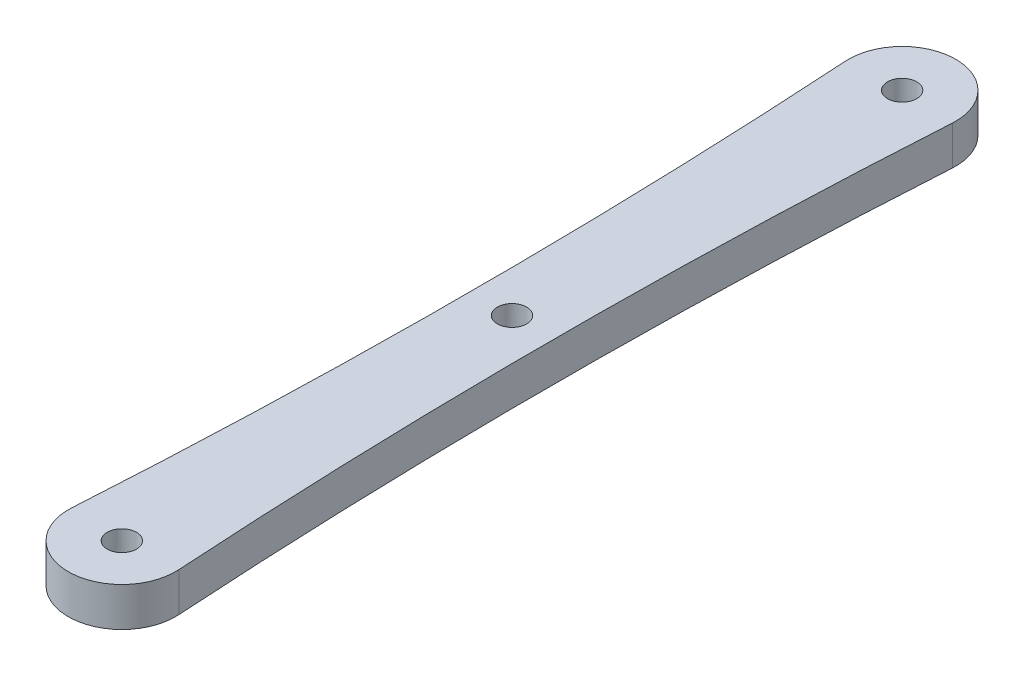
SolidWorks part; units mm, degrees
ref_plane "Front Plane" through (0, 0, 0) normal (0, 0, 1) x (1, 0, 0)
ref_plane "Top Plane" through (0, 0, 0) normal (0, 1, 0) x (1, 0, 0)
ref_plane "Right Plane" through (0, 0, 0) normal (1, 0, 0) x (0, 0, -1)
sketch "Sketch1" plane through (0, 0, 0) normal (0, 1, 0) x (1, 0, 0)
  line L0 (0, 0) -> (0, 80) construction
  line L3 (-4.25, 40) -> (4.25, 40) construction
  circle A2 centre (0, 0) radius 1.5
  circle A3 centre (0, 80) radius 1.5
  arc A8 (-5.4893, 0.3434) -> (5.4893, 0.3434) centre (0, 0) ccw
  arc A9 (5.4893, 79.6566) -> (-5.4893, 79.6566) centre (0, 80) ccw
  arc A10 (-5.4893, 79.6566) -> (-5.4893, 0.3434) centre (-639.375, 40) cw
  arc A11 (5.4893, 79.6566) -> (5.4893, 0.3434) centre (639.375, 40) ccw
  circle A12 centre (0, 40) radius 1.5
  point P3 (0, 40)
  point P16 (-4.25, 40)
  point P19 (4.25, 40)
  point P23 (0, 40)
  dimension "D1" = 3
  dimension "D2" = 80
  dimension "D3" = 4
  dimension "D5" = 3
  dimension "D4" = 8.5
extrude "Boss-Extrude1" add sketch "Sketch1" along normal blind 4
